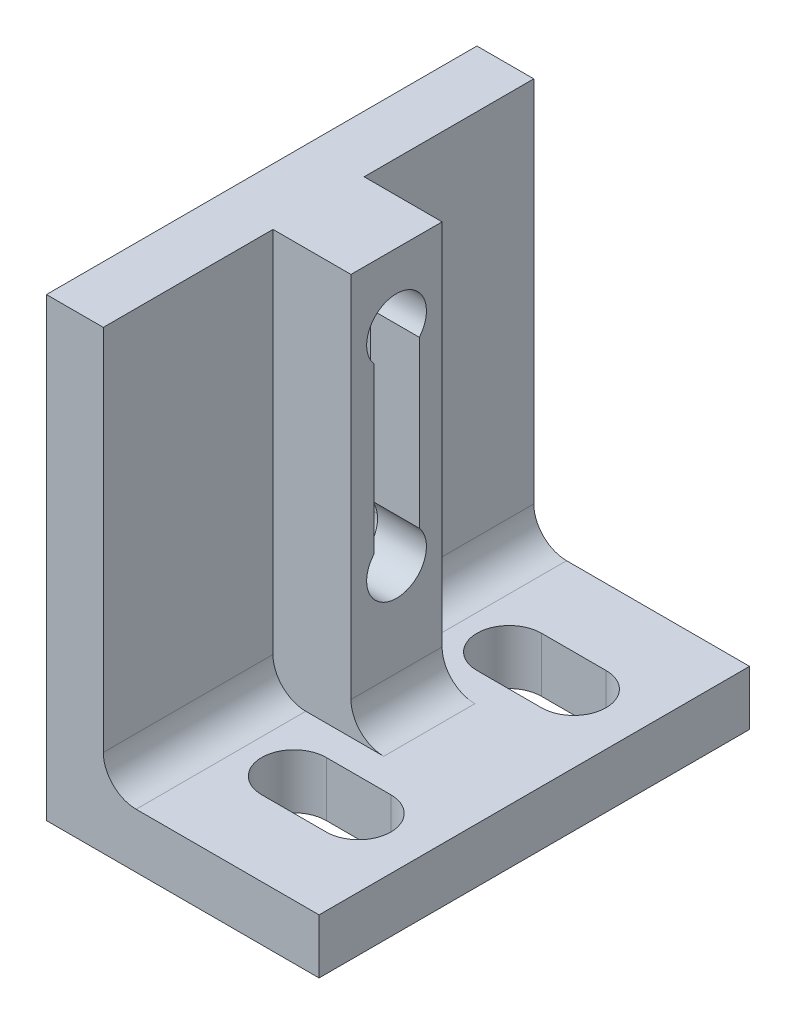
SolidWorks part; units mm, degrees
material "6061-T6 Al"
ref_plane "Front Plane" through (0, 0, 0) normal (0, 0, 1) x (1, 0, 0)
ref_plane "Top Plane" through (0, 0, 0) normal (0, 1, 0) x (1, 0, 0)
ref_plane "Right Plane" through (0, 0, 0) normal (1, 0, 0) x (0, 0, -1)
sketch "Sketch1" plane through (0, 0, 0) normal (0, 0, 1) x (1, 0, 0)
  line L0 (0, 0) -> (19, 0)
  line L1 (0, 0) -> (0, 31.75)
  dimension "D1" = 31.75
  dimension "D2" = 19
extrude "Extrude-Thin1" add sketch "Sketch1" against normal blind 30 thin thin type one direction wall 3.81
sketch "Sketch4" plane through (3.81, 0, 0) normal (1, 0, 0) x (0, 0, -1)
  line L0 (30, 0) -> (0, 0) construction
  line L3 (13.4125, 12.7) -> (13.4125, 26.924)
  line L4 (16.5875, 12.7) -> (16.5875, 26.924)
  line L6 (0, 3.81) -> (0, 31.75) construction
  arc A0 (16.5875, 26.924) -> (13.4125, 26.924) centre (15, 26.924) ccw
  arc A1 (13.4125, 12.7) -> (16.5875, 12.7) centre (15, 12.7) ccw
  dimension "D1" = 26.924
  dimension "D3" = 1.5875
  dimension "D4" = 14.224
  dimension "D2" = 15
sketch "Sketch6" plane through (0, 3.81, 0) normal (0, 1, 0) x (1, 0, 0)
  line L4 (14.2502, 24.75) -> (9.7502, 24.75)
  line L5 (9.7502, 20.25) -> (14.2502, 20.25)
  line L6 (9.7502, 9.75) -> (14.2502, 9.75)
  line L7 (14.2502, 5.25) -> (9.7502, 5.25)
  line L8 (9.7502, 7.5) -> (9.7502, 22.5) construction
  line L9 (9.7502, 22.5) -> (14.2502, 22.5) construction
  line L10 (14.2502, 22.5) -> (14.2502, 7.5) construction
  line L11 (14.2502, 7.5) -> (9.7502, 7.5) construction
  line L12 (19, 0) -> (3.81, 0) construction
  line L13 (19, 30) -> (19, 0) construction
  arc A4 (14.2502, 20.25) -> (14.2502, 24.75) centre (14.2502, 22.5) ccw
  arc A5 (9.7502, 24.75) -> (9.7502, 20.25) centre (9.7502, 22.5) ccw
  arc A6 (9.7502, 9.75) -> (9.7502, 5.25) centre (9.7502, 7.5) ccw
  arc A7 (14.2502, 5.25) -> (14.2502, 9.75) centre (14.2502, 7.5) ccw
  dimension "D1" = 7.5
  dimension "D5" = 2.25
  dimension "D2" = 15
  dimension "D3" = 4.7498
  dimension "D4" = 4.5
extrude "Extrude5" cut sketch "Sketch6" against normal through all
ref_plane "Plane1" through (0, 0, 0) normal (-1, 0, 0) x (0, 0, 1)
sketch "Sketch10" plane through (0, 0, 0) normal (0, 0, 1) x (1, 0, 0)
  line L0 (3.81, 3.81) -> (3.81, 31.75) construction
  line L1 (3.81, 31.75) -> (9.398, 31.75)
  line L2 (3.81, 31.75) -> (3.81, 3.81)
  line L3 (3.81, 3.81) -> (9.398, 3.81)
  line L4 (9.398, 31.75) -> (9.398, 3.81)
  line L5 (19, 3.81) -> (3.81, 3.81) construction
  line L6 (0, 31.75) -> (3.81, 31.75) construction
  dimension "D1" = 5.588
extrude "Boss-Extrude1" add sketch "Sketch10" against normal up to surface (30 mm away) up to face at (7.6033, 11.8533, -30)
extrude "Cut-Extrude1" cut sketch "Sketch4" against normal through all and the other way through all
sketch "Sketch11" plane through (0, 0, 5.175) normal (1, 0, 0) x (0, 0, -1)
  line L0 (20.175, 26.924) -> (20.175, 12.7) construction
  line L3 (17.8001, 12.7) -> (17.8001, 26.924)
  line L4 (22.5499, 12.7) -> (22.5499, 26.924)
  arc A0 (22.5499, 26.924) -> (17.8001, 26.924) centre (20.175, 26.924) ccw
  arc A1 (17.8001, 12.7) -> (22.5499, 12.7) centre (20.175, 12.7) ccw
  arc A2 (21.7625, 26.924) -> (18.5875, 26.924) centre (20.175, 26.924) ccw construction
  arc A3 (18.5875, 12.7) -> (21.7625, 12.7) centre (20.175, 12.7) ccw construction
  dimension "D3" = 2.3749
hole_wizard "#8-32 Tapped Hole1" positions "Sketch13" profile "Sketch12" tap size "#8-32" standard "ANSI Inch" end condition through all
sketch "Sketch13" plane through (9.398, 0, 0) normal (1, 0, 0) x (0, 0, -1)
  point P4 (15, 12.7)
  point P7 (15, 26.924)
sketch "Sketch12" plane through (9.398, 12.7, -15) normal (0, 1, 0) x (0, 0, -1)
  line L0 (0, 0) -> (0, 9.398)
  line L1 (0, 9.398) -> (2.0828, 9.398)
  line L2 (2.0828, 9.398) -> (2.0828, 0)
  line L5 (2.0828, 0) -> (0, 0)
  line L11 (0, -6.35) -> (0, 107.95) construction
  dimension "Thread Major Dia." = 4.1656
  dimension "Thru Tap Drill Depth" = 9.398
sketch "Sketch14" plane through (0, 31.75, 0) normal (0, 1, 0) x (1, 0, 0)
  line L0 (0, 16.5) -> (0, -16.5) construction
  line L1 (9.398, 30) -> (3.9624, 30)
  line L2 (9.398, 30) -> (9.398, 18.175)
  line L3 (9.398, 18.175) -> (3.9624, 18.175)
  line L4 (3.9624, 30) -> (3.9624, 18.175)
  line L5 (9.398, 0) -> (3.9624, 0)
  line L6 (9.398, 0) -> (9.398, 11.825)
  line L7 (9.398, 11.825) -> (3.9624, 11.825)
  line L8 (3.9624, 0) -> (3.9624, 11.825)
  line L9 (3.9624, 18.175) -> (3.9624, 11.825) construction
  line L10 (0, 15) -> (3.9624, 15) construction
  line L11 (0, 12.6251) -> (0, 17.3749) construction
  dimension "D1" = 3.9624
  dimension "D2" = 6.35
extrude "Cut-Extrude2" cut sketch "Sketch14" against normal up to surface (27.94 mm away) up to face at (12.1805, 3.81, -15)
fillet "Fillet1" radius 2.286 1 edges at (9.398, 3.81, -15)
fillet "Fillet2" radius 2.286 2 edges at (3.9624, 3.81, -5.9125) (3.9624, 3.81, -24.0875)
extrude "Cut-Extrude3" cut sketch "Sketch11" along normal blind 5.9944
